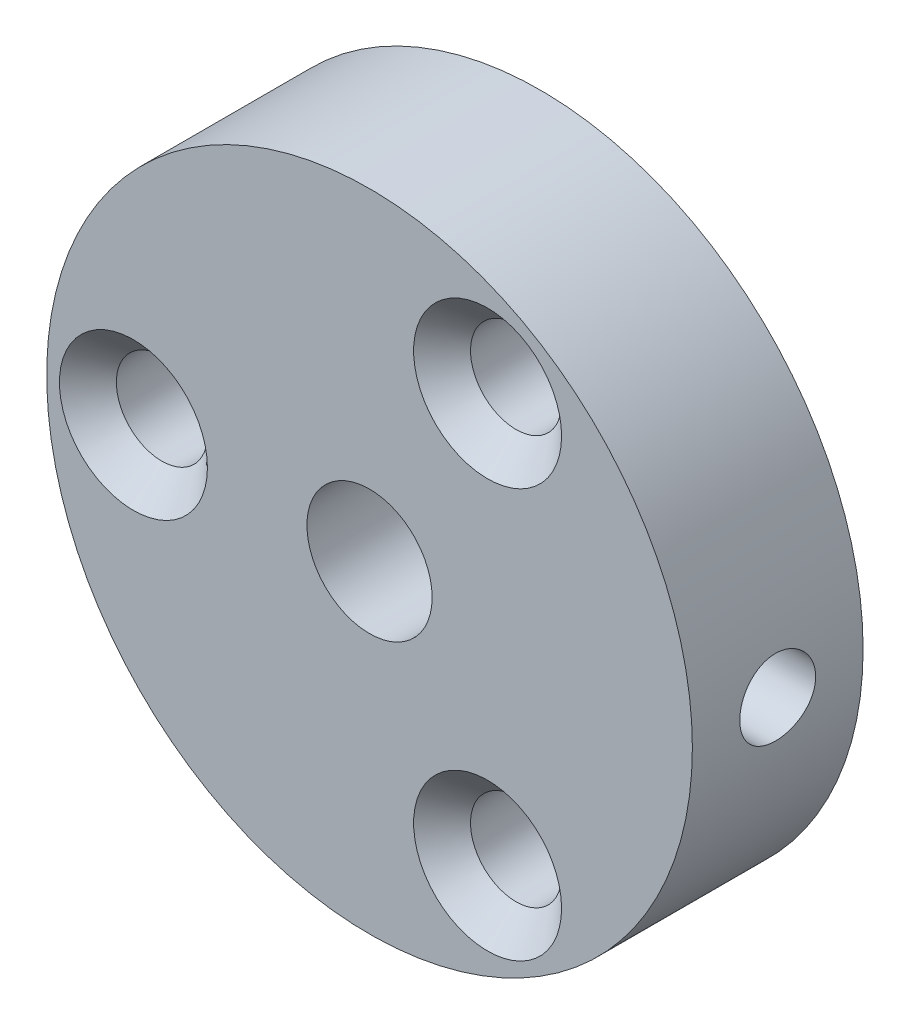
SolidWorks part; units mm, degrees
ref_plane "Front Plane" through (0, 0, 0) normal (0, 0, 1) x (1, 0, 0)
ref_plane "Top Plane" through (0, 0, 0) normal (0, 1, 0) x (1, 0, 0)
ref_plane "Right Plane" through (0, 0, 0) normal (1, 0, 0) x (0, 0, -1)
sketch "Sketch2" plane through (0, 0, 0) normal (0, 0, 1) x (1, 0, 0)
  circle A0 centre (0, 0) radius 8.509
  dimension "D1" = 17.018
extrude "Boss-Extrude1" add sketch "Sketch2" along normal mid plane 4.5
ref_plane "Plane1" through (0, 0, 2.25) normal (0, 0, 1) x (1, 0, 0)
sketch "Sketch3" plane through (0, 0, 2.25) normal (0, 0, 1) x (1, 0, 0)
  line L0 (-8.509, 0) -> (8.509, 0) construction
  circle A0 centre (0, 0) radius 6.223 construction
  circle A2 centre (0, 0) radius 8.509 construction
  circle A3 centre (-6.223, 0) radius 1.143
  circle A4 centre (3.1115, 5.3893) radius 1.143
  circle A5 centre (3.1115, -5.3893) radius 1.143
  point P16 (0, 0)
  dimension "D1" = 12.446
  dimension "D2" = 2.286
  dimension "D4" = 5.3893
  dimension "D5" = 3.1115
  dimension "D3" = 3
hole_wizard "M2 Clearance Hole1" positions "Sketch6" profile "Sketch7" hole size "M2" standard "ANSI Metric" end condition through all
sketch "Sketch6" plane through (0, 0, 2.25) normal (0, 0, 1) x (1, 0, 0)
  point P0 (-6.223, 0)
  point P3 (3.1115, 5.3893)
  point P6 (3.1115, -5.3893)
sketch "Sketch7" plane through (-6.223, 0, 2.25) normal (1, 0, 0) x (0, -1, 0)
  line L0 (0, 0) -> (0, 4.5)
  line L1 (0, 4.5) -> (1.2, 4.5)
  line L2 (1.2, 4.5) -> (1.2, 0)
  line L5 (1.2, 0) -> (0, 0)
  line L11 (0, -6.35) -> (0, 107.95) construction
  dimension "Thru Hole Dia." = 2.4
  dimension "Thru Hole Depth" = 4.5
chamfer "Chamfer1" distance 0.75 angle 45 1 edges at (4.3115, -5.3893, 2.25)
chamfer "Chamfer2" distance 0.75 angle 45 1 edges at (4.3115, 5.3893, 2.25)
chamfer "Chamfer3" distance 0.75 angle 45 1 edges at (-5.023, 0, 2.25)
hole_wizard "M4x0.7 Tapped Hole1" positions "Sketch8" profile "Sketch9" tap size "M4x0.7" standard "ANSI Metric" end condition through all
sketch "Sketch8" plane through (0, 0, 2.25) normal (0, 0, 1) x (1, 0, 0)
  point P0 (0, 0)
sketch "Sketch9" plane through (0, 0, 2.25) normal (1, 0, 0) x (0, -1, 0)
  line L0 (0, 0) -> (0, 4.5)
  line L1 (0, 4.5) -> (1.65, 4.5)
  line L2 (1.65, 4.5) -> (1.65, 0)
  line L5 (1.65, 0) -> (0, 0)
  line L11 (0, -6.35) -> (0, 107.95) construction
  dimension "Thru Tap Drill Dia." = 3.3
  dimension "Thru Tap Drill Depth" = 4.5
cosmetic thread "Hole Thread1"
ref_plane "Plane2" through (5, 0, 0) normal (1, 0, 0) x (0, 0, -1)
sketch "Sketch11" plane through (5, 0, 0) normal (1, 0, 0) x (0, 0, -1)
  circle A0 centre (0, 0) radius 1
  dimension "D1" = 2
extrude "Cut-Extrude1" cut sketch "Sketch11" along normal through all
